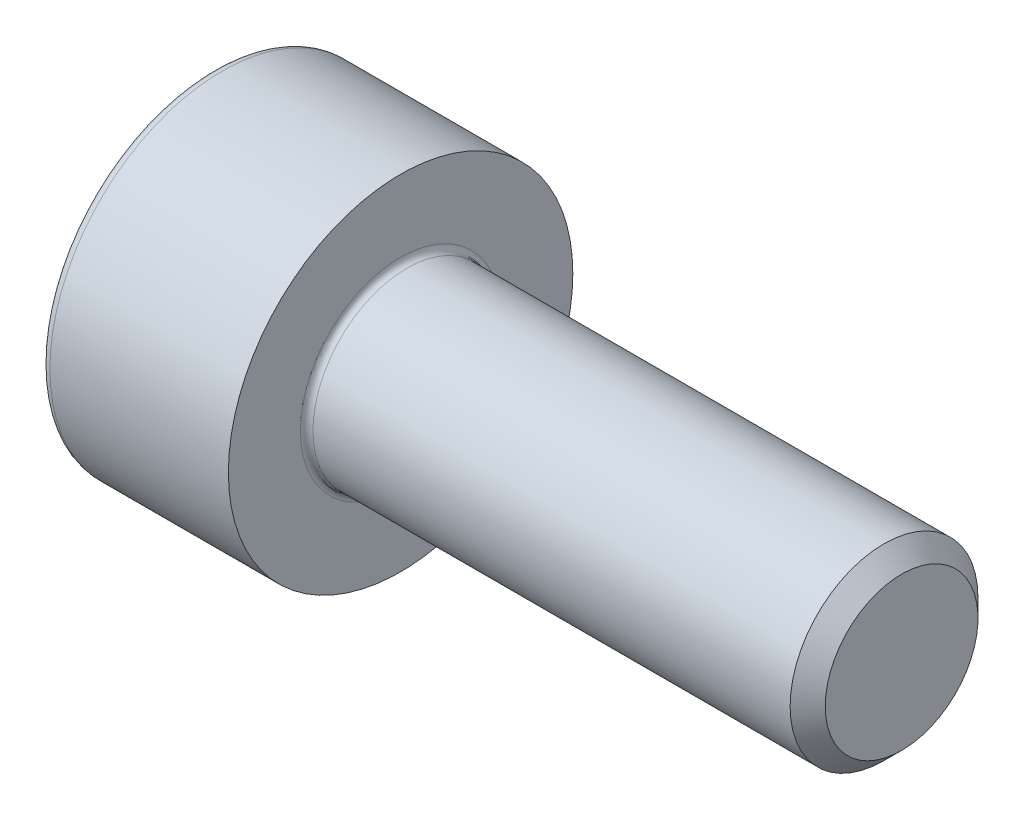
SolidWorks part; units mm, degrees
revolve "Base-Revolve" add sketch "BodySke"
sketch "BodySke" plane through (0, 0, 0) normal (0, 0, 1) x (1, 0, 0)
  line L0 (0, 0) -> (0, 2.75)
  line L1 (0, 2.75) -> (3, 2.75)
  line L2 (3, 2.75) -> (3, 1.5)
  line L3 (3, 1.5) -> (10.7195, 1.5)
  line L4 (11, 1.2195) -> (11, 0)
  line L5 (11, 0) -> (0, 0)
  line L6 (-31.75, 0) -> (127, 0) construction
  line L8 (11, 1.2195) -> (10.7195, 1.5)
  line L10 (11, -1.2195) -> (10.7195, -1.5) construction
  line L11 (3.5, 9.525) -> (3.5, 3.175) construction
  line L12 (6, 9.525) -> (6, 3.175) construction
  line L13 (-49, 9.525) -> (-49, 3.175) construction
  dimension "Head_ht" = 3
  dimension "Length" = 8
  dimension "Body_ch_ang" = 45
  dimension "Diameter" = 3
  dimension "Minor_dia" = 2.439
  dimension "Advance" = 0.5
  dimension "Thread_nom" = 5
  dimension "Thread_length" = 60
  dimension "Head_dia" = 5.5
cosmetic thread "ThreadCosmetic" [suppressed]
fillet "Fillet1" radius 0.1 1 edges at (3, 0, 1.5)
fillet "Fillet2" radius 0.15 1 edges at (0, 0, 2.75)
ref_plane "Plane1" through (0, 0, 0) normal (0, 0, 1) x (1, 0, 0)
ref_plane "Plane2" through (0, 0, 0) normal (0, 1, 0) x (1, 0, 0)
ref_plane "Plane3" through (0, 0, 0) normal (1, 0, 0) x (0, 0, -1)
sketch "Sketch2" plane through (0, 0, 0) normal (0, 0, 1) x (1, 0, 0)
  line L0 (0, 1.28) -> (1.3, 1.28)
  line L1 (1.3, 1.28) -> (2.039, 0)
  line L2 (-31.75, 0) -> (127, 0) construction
  line L3 (2.039, 0) -> (0, 0)
  line L4 (0, 0) -> (0, 1.28)
  line L6 (0, 0) -> (47.625, 0) construction
  dimension "D1" = 1.28
  dimension "D2" = 60
  dimension "Depth" = 1.3
revolve "Hex-PreBroach" cut sketch "Sketch2" angle 360 about L6
sketch "Sketch3" plane through (0, 0, 0) normal (-1, 0, 0) x (0, 0.5, 0.866)
  line L0 (0.739, 1.28) -> (-0.739, 1.28)
  line L1 (-0.739, 1.28) -> (-1.478, 0)
  line L2 (0.739, 1.28) -> (1.478, 0)
  line L3 (0.739, -1.28) -> (1.478, 0)
  line L4 (0.739, -1.28) -> (-0.739, -1.28)
  line L5 (-0.739, -1.28) -> (-1.478, 0)
  dimension "D1" = 1.28
  dimension "D2" = 1.28
  dimension "Hex_size" = 2.56
extrude "Hex" cut sketch "Sketch3" against normal blind 1.3
sketch "ThdSchSke" plane through (0, 0, 0) normal (0, 0, 1) x (1, 0, 0)
  line L0 (6, -1.2195) -> (5.8036, -1.5)
  line L1 (6, -1.2195) -> (6.1964, -1.5)
  line L2 (6.1964, -1.5) -> (6.1964, -1.875)
  line L3 (-3.175, 0) -> (5.1513, 0) construction
  line L4 (0, 2.6) -> (0, -2.6) construction
  line L5 (6.1964, -1.875) -> (5.8036, -1.875)
  line L6 (5.8036, -1.875) -> (5.8036, -1.5)
  dimension "Thread_minor" = 2.439
  dimension "Diameter" = 3
  dimension "Start" = 6
revolve "ThreadSchematic" [suppressed] cut sketch "ThdSchSke" angle 360 about L3
pattern_linear "ThdSchPat" [suppressed]
equation "\"D2@Sketch3\" = \"Hex_size@Sketch3\" / 2"
equation "\"D1@Sketch3\" = \"Hex_size@Sketch3\" / 2"
equation "\"D1@Sketch2\" = \"Hex_size@Sketch3\" / 2"
equation "\"Thread_minor@ThreadCosmetic\"  =  \"Minor_dia@BodySke\""
equation "\"Depth@Sketch2\" =  \"Key_eng@Hex\""
equation "\"Thread_length@ThreadCosmetic\" = ((sgn( (\"Length@BodySke\" - \"Advance@BodySke\" * 3.0) - \"Thread_nom@BodySke\" )-1)*( (\"Length@BodySke\" - \"Advance@BodySke\" * 3.0) - \"Thread_nom@BodySke\" ))/-2+ \"Thread_nom@BodySke\""
equation "\"Thread_minor@ThdSchSke\" = \"Minor_dia@BodySke\""
equation "\"Diameter@ThdSchSke\" = \"Diameter@BodySke\""
equation "\"Overcut@ThdSchSke\" = \"Diameter@BodySke\" * 1.25"
equation "\"Start@ThdSchSke\" = \"Head_ht@BodySke\" + \"Length@BodySke\" - \"Thread_length@ThreadCosmetic\"  '---Non-countersunk---"
equation "\"Num_threads@ThdSchPat\" = int( \"Thread_length@ThreadCosmetic\" / \"Advance@BodySke\" + 0.999 )  + 1"
equation "\"Advance@ThdSchPat\" = \"Thread_length@ThreadCosmetic\" /  (\"Num_threads@ThdSchPat\" - 1) 'relax it"
equation "\"Num_threads@ThdSchPat\" = \"Num_threads@ThdSchPat\" - sgn( \"Num_threads@ThdSchPat\" - 1) '---chamfered tips only---"
